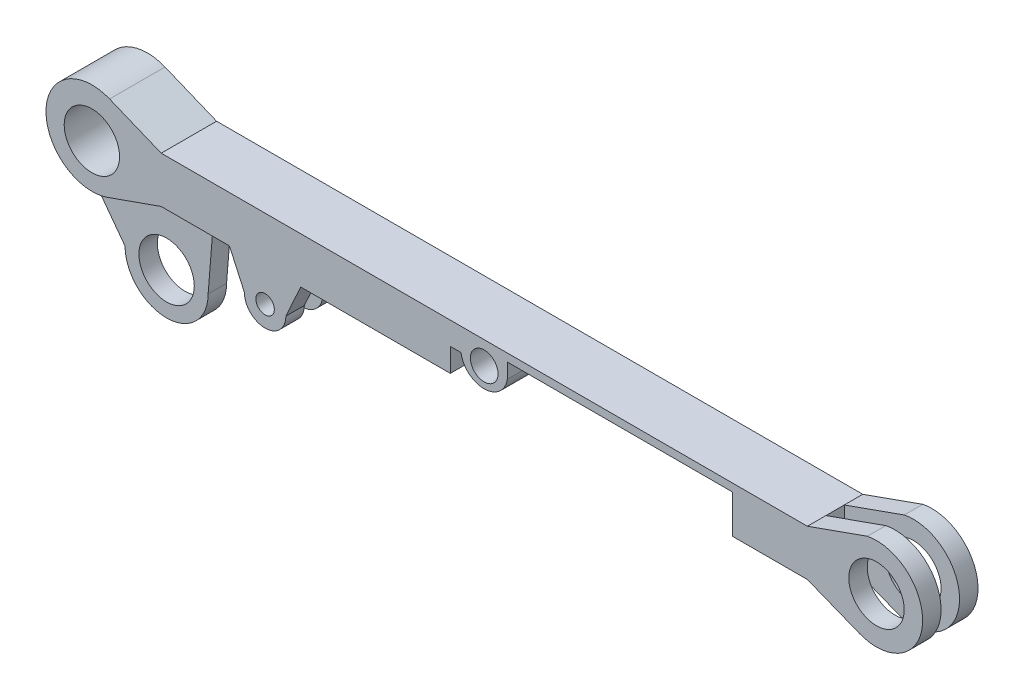
SolidWorks part; units mm, degrees
ref_plane "Front Plane" through (0, 0, 0) normal (0, 0, 1) x (1, 0, 0)
ref_plane "Top Plane" through (0, 0, 0) normal (0, 1, 0) x (1, 0, 0)
ref_plane "Right Plane" through (0, 0, 0) normal (1, 0, 0) x (0, 0, -1)
sketch "Sketch1" plane through (0, 0, 0) normal (0, 0, 1) x (1, 0, 0)
  line L0 (-349.8733, 24.6435) -> (-405.7801, 47.538)
  line L1 (350.1267, -25.3565) -> (-349.8733, -25.3565)
  line L3 (350.1267, 24.6435) -> (-349.8733, 24.6435)
  line L7 (-349.8733, -25.3565) -> (-408.1023, -45.8872)
  line L9 (0.1267, 24.6435) -> (350.1267, 24.6435) construction
  line L10 (350.1267, 24.6435) -> (415.1579, 47.7515)
  line L11 (350.1267, -25.3565) -> (406.5613, -47.7462)
  line L14 (-349.8733, 24.6435) -> (0.1267, 24.6435) construction
  arc A0 (-405.7801, 47.538) -> (-408.1023, -45.8872) centre (-424.7285, 1.2675) ccw
  arc A1 (406.5613, -47.7462) -> (401.7026, 42.9703) centre (425, -1.2703) ccw
  point P0 (0, 0)
  dimension "D4" = 100
  dimension "D5" = 100
  dimension "D1" = 700
  dimension "D2" = 50
extrude "Boss-Extrude1" add sketch "Sketch1" along normal blind 300 contours L11 A1 L10 L3 L0 A0 L7 L1
sketch "Sketch2" plane through (0, 24.6435, 0) normal (0, 1, 0) x (1, 0, 0)
  line L0 (475, -124.9235) -> (350.1267, -124.9235)
  line L1 (-474.7285, -184.9235) -> (-474.7285, -164.9235)
  line L2 (-474.7285, 0) -> (-474.7285, -300) construction
  line L3 (350.1267, -124.9235) -> (273.7, -124.9235)
  line L4 (273.7, -124.9235) -> (-0.1846, -124.9235)
  line L5 (-0.1846, -124.9235) -> (-274.0692, -124.9235)
  line L6 (-274.0692, -124.9235) -> (-349.8733, -124.9235)
  line L7 (-474.7285, -164.9235) -> (-349.8733, -164.9235)
  line L8 (-349.8733, -124.9235) -> (-474.7285, -124.9235)
  line L9 (-349.8733, -300) -> (-349.8733, 0) construction
  line L10 (475, -144.9235) -> (350.1267, -144.9235)
  line L11 (350.1267, -144.9235) -> (273.7, -144.9235)
  line L12 (273.7, -144.9235) -> (273.7, -164.9235)
  line L13 (475, -124.9235) -> (475, -144.9235)
  line L14 (273.7, -164.9235) -> (350.1267, -164.9235)
  line L15 (350.1267, -164.9235) -> (479.1454, -164.9235)
  line L16 (479.1454, -164.9235) -> (479.1454, -184.9235)
  line L17 (479.1454, -184.9235) -> (350.1267, -184.9235)
  line L18 (350.1267, -184.9235) -> (273.7, -184.9235)
  line L19 (273.7, -184.9235) -> (-274.0692, -184.9235)
  line L20 (-274.0692, -184.9235) -> (-349.8733, -184.9235)
  line L21 (-349.8733, -184.9235) -> (-474.7285, -184.9235)
  line L22 (-474.7285, -124.9235) -> (-474.7285, -144.9235)
  line L23 (-474.7285, -144.9235) -> (-349.8733, -144.9235)
  line L24 (-349.8733, -144.9235) -> (-274.0692, -144.9235)
  line L25 (-274.0692, -144.9235) -> (-274.0692, -164.9235)
  line L26 (-274.0692, -164.9235) -> (-349.8733, -164.9235)
  line L27 (-274.0692, -124.9235) -> (-274.0692, -184.9235) construction
  line L28 (273.7, -184.9235) -> (273.7, -124.9235) construction
  line L29 (350.1267, -300) -> (350.1267, 0) construction
  line L30 (-353.4971, -124.9235) -> (369.4184, -124.9235) construction
  line L31 (-412.3009, -184.9235) -> (588.4203, -184.9235) construction
  line L32 (-349.8733, -164.9235) -> (734.5977, -164.9235) construction
  line L33 (-349.8733, -144.9235) -> (552.8227, -144.9235) construction
  line L34 (-0.1846, -124.9235) -> (-0.1846, -184.9235) construction
  line L35 (-0.1846, -154.9235) -> (-274.0692, -154.9235) construction
  line L36 (-274.0692, -154.9235) -> (273.7, -154.9235) construction
  dimension "D1" = 20
  dimension "D2" = 20
  dimension "D3" = 20
  dimension "D4" = 20
extrude "Cut-Extrude1" cut sketch "Sketch2" against normal blind 1000 flip side to cut
sketch "Sketch4" plane through (0, 24.6435, 0) normal (0, 1, 0) x (1, 0, 0)
  line L1 (-474.7285, -144.9235) -> (-274.0692, -144.9235)
  line L2 (-274.0692, -144.9235) -> (-274.0692, -164.9235)
  line L3 (-274.0692, -164.9235) -> (-474.7285, -164.9235)
  line L9 (350.1267, -184.9235) -> (273.7, -184.9235)
  line L10 (-349.8733, -184.9235) -> (350.1267, -184.9235) construction
  line L11 (273.7, -184.9235) -> (350.1267, -184.9235)
  line L12 (350.1267, -184.9235) -> (475, -184.9235)
  line L13 (475, -184.9235) -> (475, -164.9235)
  line L14 (475, -164.9235) -> (350.1267, -164.9235)
  line L15 (350.1267, -164.9235) -> (350.1267, -144.9235)
  line L16 (350.1267, -144.9235) -> (475, -144.9235)
  line L17 (475, -144.9235) -> (475, -124.9235)
  line L18 (475, -124.9235) -> (350.1267, -124.9235)
  line L23 (-349.8733, -124.9235) -> (475, -124.9235)
  line L24 (475, -124.9235) -> (475, -144.9235)
  line L25 (475, -144.9235) -> (273.7, -144.9235)
  line L26 (273.7, -144.9235) -> (273.7, -164.9235)
  line L27 (273.7, -164.9235) -> (475, -164.9235)
  line L28 (475, -164.9235) -> (475, -184.9235)
  line L29 (475, -184.9235) -> (273.7, -184.9235)
  line L30 (350.1267, -184.9235) -> (-474.7285, -184.9235)
  line L31 (-474.7285, -184.9235) -> (-474.7285, -164.9235)
  line L32 (-474.7285, -164.9235) -> (-274.0692, -164.9235)
  line L33 (-274.0692, -144.9235) -> (-474.7285, -144.9235)
  line L34 (-474.7285, -124.9235) -> (-474.7285, -144.9235) construction
  line L35 (-474.7285, -144.9235) -> (-474.7285, -124.9235)
  line L36 (-474.7285, -124.9235) -> (-349.8733, -124.9235)
sketch "Sketch31" plane through (0, 24.6435, 0) normal (0, 1, 0) x (1, 0, 0)
  line L0 (-474.7285, -124.9235) -> (475, -124.9235)
  line L1 (475, -124.9235) -> (475, -144.9235)
  line L2 (475, -144.9235) -> (273.7, -144.9235)
  line L3 (273.7, -144.9235) -> (273.7, -164.9235)
  line L4 (273.7, -164.9235) -> (475, -164.9235)
  line L5 (475, -164.9235) -> (475, -184.9235)
  line L6 (475, -184.9235) -> (-474.7285, -184.9235)
  line L7 (-474.7285, -184.9235) -> (-474.7285, -164.9235)
  line L8 (-474.7285, -164.9235) -> (-274.0692, -164.9235)
  line L9 (-274.0692, -164.9235) -> (-274.0692, -144.9235)
  line L10 (-274.0692, -144.9235) -> (-474.7285, -144.9235)
  line L11 (-474.7285, -144.9235) -> (-474.7285, -124.9235)
extrude "Cut-Extrude13" cut sketch "Sketch31" against normal mid plane 500 flip side to cut
sketch "Sketch5" plane through (0, 0, 184.9235) normal (0, 0, 1) x (1, 0, 0)
  circle A0 centre (425, -1.2703) radius 30
sketch "Sketch32" plane through (0, 24.6435, 0) normal (0, 1, 0) x (1, 0, 0)
  line L0 (331.432, -144.9235) -> (331.432, -164.9235)
  line L1 (273.7, -144.9235) -> (350.1267, -144.9235) construction
  line L2 (350.1267, -164.9235) -> (273.7, -164.9235) construction
sketch "Sketch33" plane through (0, 0, 184.9235) normal (0, 0, 1) x (1, 0, 0)
  circle A0 centre (425, -1.2703) radius 30
extrude "Cut-Extrude14" cut sketch "Sketch33" against normal up to surface (60 mm away) up to face at (0.5638, -0.4801, 124.9235)
mirror "Mirror2" about plane through (0, 0, 0) normal (1, 0, 0) of "Cut-Extrude14"
sketch "Sketch34" plane through (0, -25.3565, 0) normal (0, -1, 0) x (1, 0, 0)
  line L1 (-349.8733, 164.9235) -> (-274.0692, 164.9235)
  line L2 (-349.8733, 164.9235) -> (-349.8733, 144.9235)
  line L3 (-349.8733, 144.9235) -> (-274.0692, 144.9235)
  line L4 (-274.0692, 164.9235) -> (-274.0692, 144.9235)
extrude "Boss-Extrude8" add sketch "Sketch34" against normal up to surface (50 mm away) up to face at (0.0229, 24.6435, 154.9235)
sketch "Sketch36" plane through (0, 0, 184.9235) normal (0, 0, 1) x (1, 0, 0)
  line L0 (-474.713, 2.51) -> (0, 0) construction
  line L1 (-237.3565, 1.255) -> (-237.3565, -25.3565) construction
  line L2 (350.1267, -25.3565) -> (-349.8733, -25.3565) construction
  line L3 (-275.9506, -25.3565) -> (-259.8565, -60.7302)
  line L4 (-275.9506, -25.3565) -> (-237.3565, -25.3565) construction
  line L5 (-237.3565, -25.3565) -> (-198.7624, -25.3565) construction
  line L6 (-198.7624, -25.3565) -> (-214.8565, -60.7302)
  line L7 (-275.9506, -25.3565) -> (-198.7624, -25.3565)
  arc A0 (-405.7801, 47.538) -> (-408.1023, -45.8872) centre (-424.7285, 1.2675) ccw construction
  circle A1 centre (-237.3565, -60.7302) radius 22.5
  circle A2 centre (-237.3565, -60.7302) radius 10
  line M9 (-349.8733, -25.3565) -> (350.1267, -25.3565)
extrude "Boss-Extrude9" add sketch "Sketch36" against normal up to surface (60 mm away) contours A1 L6 L3 M9 | A1 A2 up to face at (-455, -1.2703, 124.9235)
sketch "Sketch37" plane through (0, 0, 184.9235) normal (0, 0, 1) x (1, 0, 0)
  circle A0 centre (0, 0) radius 15
extrude "Cut-Extrude15" cut sketch "Sketch37" against normal up to surface (60 mm away) up to face at (-455, -1.2703, 124.9235)
sketch "Sketch6" plane through (0, 0, 184.9235) normal (0, 0, 1) x (1, 0, 0)
  circle A0 centre (0, 0) radius 15
sketch "Sketch8" plane through (0, 0, 184.9235) normal (0, 0, 1) x (1, 0, 0)
  line L0 (0, 0) -> (-225, 0) construction
  line L1 (-231.7306, -25.3565) -> (-230.625, -44.9024)
  line L2 (949.8642, -25.3565) -> (-949.5927, -25.3565) construction
  line L3 (-218.2694, -25.3565) -> (-219.375, -44.9024)
  line L4 (-231.7306, -25.3565) -> (-225, -25.3565)
  line L5 (-225, -25.3565) -> (-218.2694, -25.3565)
  line L6 (-225, 0) -> (-225, -25.3565) construction
  line L7 (-235.6987, -21.6065) -> (-234.3742, -45.0218)
  line L8 (-214.3013, -21.6065) -> (-215.6258, -45.0218)
  line L9 (-225, -21.6065) -> (-214.3013, -21.6065)
  line L10 (-235.6987, -21.6065) -> (-225, -21.6065)
  arc A0 (-230.625, -44.9024) -> (-219.375, -44.9024) centre (-225, -44.9024) ccw
  arc A1 (-234.3742, -45.0218) -> (-215.6258, -45.0218) centre (-225, -44.9024) ccw
  dimension "D2" = 3.75
  dimension "D3" = 5.625
  dimension "D1" = 225
sketch "Sketch40" plane through (-349.8733, 0, 0) normal (-1, 0, 0) x (0, 0, 1)
  line L0 (144.9235, -25.3565) -> (164.9235, -25.3565)
  line L1 (164.9235, -25.3565) -> (164.9235, -86.0189)
  line L2 (164.9235, -86.0189) -> (144.9235, -86.0189)
  line L3 (144.9235, -86.0189) -> (144.9235, -25.3565)
extrude "Cut-Extrude16" cut sketch "Sketch40" against normal blind 190
sketch "Sketch41" plane through (0, 0, 164.9235) normal (0, 0, -1) x (-1, 0, 0)
  line L3 (349.8733, 24.6435) -> (349.8733, -25.3565)
  line L4 (349.8733, -25.3565) -> (408.1023, -45.8872)
  line L5 (405.7801, 47.538) -> (349.8733, 24.6435)
  line L6 (349.8733, 24.6435) -> (349.8733, -25.3565)
  line L7 (349.8733, -25.3565) -> (408.1023, -45.8872)
  line L8 (405.7801, 47.538) -> (349.8733, 24.6435)
  arc A1 (408.1023, -45.8872) -> (405.7801, 47.538) centre (424.7285, 1.2675) ccw
  arc A2 (408.1023, -45.8872) -> (405.7801, 47.538) centre (424.7285, 1.2675) ccw
  dimension "D1" = 0
extrude "Boss-Extrude10" add sketch "Sketch41" along normal up to surface (20 mm away) up to face at (-395.3502, 0.6556, 144.9235)
sketch "Sketch42" plane through (0, 0, 144.9235) normal (0, 0, -1) x (-1, 0, 0)
  circle A1 centre (425, -1.2703) radius 30
  circle A2 centre (425, -1.2703) radius 30
  dimension "D1" = 0
extrude "Cut-Extrude17" cut sketch "Sketch42" against normal blind 190
sketch "Sketch43" plane through (0, 0, 144.9235) normal (0, 0, 1) x (1, 0, 0)
  line L0 (-458.7384, -35.3838) -> (-409.0656, -102.0595)
  line L1 (-319.0656, -102.0595) -> (-312.912, -25.3565)
  line L2 (-275.9506, -25.3565) -> (-349.8733, -25.3565) construction
  line L3 (-408.1023, -45.8872) -> (-349.8733, -25.3565)
  line L4 (-349.8733, -25.3565) -> (-312.912, -25.3565)
  circle A0 centre (-364.0656, -102.0595) radius 30
  circle A1 centre (-364.0656, -102.0595) radius 45
  arc A2 (-405.7801, 47.538) -> (-408.1023, -45.8872) centre (-424.7285, 1.2675) ccw construction
  arc A3 (-458.7384, -35.3838) -> (-408.1023, -45.8872) centre (-424.7285, 1.2675) ccw
extrude "Boss-Extrude11" add sketch "Sketch43" along normal blind 20 contours A3 L0 A1 L1 L4 L3 | A1 A0
sketch "Sketch16" plane through (0, 24.6435, 0) normal (0, 1, 0) x (1, 0, 0)
  line L0 (350.1267, -144.9235) -> (350.1267, -164.9235)
  line L1 (350.1267, -164.9235) -> (273.7, -164.9235)
  line L2 (273.7, -164.9235) -> (273.7, -144.9235)
  line L3 (273.7, -144.9235) -> (350.1267, -144.9235)
extrude "Boss-Extrude5" add sketch "Sketch16" against normal up to surface (50 mm away) up to face at (-98.8131, -25.3565, 154.9235)
sketch "Sketch23" plane through (0, 0, 184.9235) normal (0, 0, 1) x (1, 0, 0)
  line L0 (0, 0) -> (-337.5, 0) construction
  dimension "D1" = 337.5
sketch "Sketch44" plane through (0, 0, 184.9235) normal (0, 0, 1) x (1, 0, 0)
  line L0 (-25.1605, 0) -> (-36.6581, 0)
  line L1 (-36.6581, 0) -> (-36.6581, -25.3565)
  line L2 (350.1267, -25.3565) -> (-198.7624, -25.3565) construction
  line L3 (25.0883, 0) -> (25.0883, 16.213)
  line L4 (25.0883, 16.213) -> (269.2537, 16.213)
  line L5 (269.2537, 16.213) -> (269.2537, -25.3565)
  line L6 (269.2537, -25.3565) -> (-36.6581, -25.3565)
  arc A0 (-25.1605, 0) -> (25.0883, 0) centre (-0.0361, 3.8904) ccw
extrude "Cut-Extrude18" cut sketch "Sketch44" against normal up to surface (60 mm away) up to face at (-15, 0, 124.9235)
